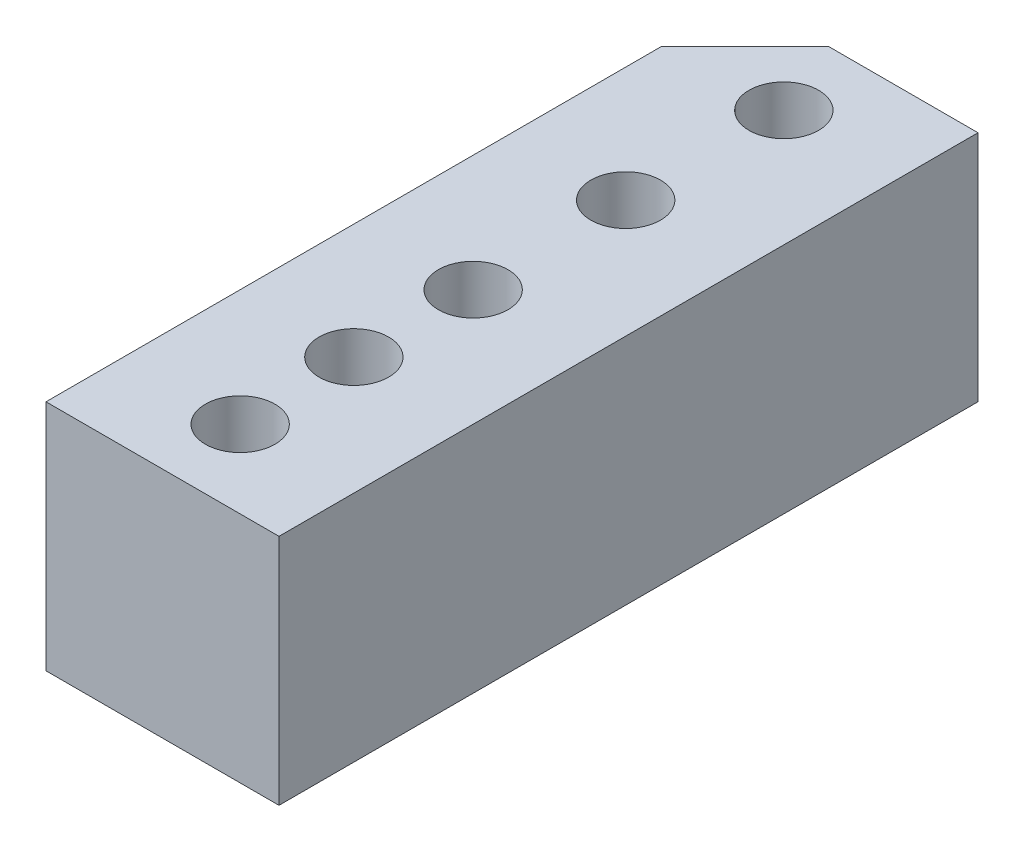
SolidWorks part; units mm, degrees
ref_plane "Front Plane" through (0, 0, 0) normal (0, 0, 1) x (1, 0, 0)
ref_plane "Top Plane" through (0, 0, 0) normal (0, 1, 0) x (1, 0, 0)
ref_plane "Right Plane" through (0, 0, 0) normal (1, 0, 0) x (0, 0, -1)
sketch "Sketch1" plane through (0, 0, 0) normal (0, 0, 1) x (1, 0, 0)
  line L1 (-4.7625, -4.7625) -> (4.7625, -4.7625)
  line L2 (-4.7625, -4.7625) -> (-4.7625, 4.7625)
  line L3 (-4.7625, 4.7625) -> (4.7625, 4.7625)
  line L4 (4.7625, -4.7625) -> (4.7625, 4.7625)
  line L5 (-4.7625, -4.7625) -> (4.7625, 4.7625) construction
  line L6 (-4.7625, 4.7625) -> (4.7625, -4.7625) construction
  point P0 (0, 0)
  dimension "D1" = 9.525
extrude "Extrude1" add sketch "Sketch1" along normal blind 28.575
hole_wizard "#4-40 Tapped Hole1" positions "3DSketch1" profile "Sketch2" tap size "#4-40" standard "Ansi Inch" end condition through all
sketch3d "3DSketch1"
  line L1 (-4.7625, 4.7625, 28.575) -> (-4.7625, 4.7625, 0) construction
  line L2 (4.7625, 4.7625, 28.575) -> (-4.7625, 4.7625, 28.575) construction
  point P0 (0, 4.7625, 3.175)
  point P2 (0, 4.7625, 15.875)
  point P4 (0, 4.7625, 25.4)
  dimension "D1" = 12.7
  dimension "D2" = 9.525
  dimension "D3" = 3.175
  dimension "D4" = 4.7625
sketch "Sketch2" plane through (0, 4.7625, 3.175) normal (1, 0, 0) x (0, 0, 1)
  line L0 (0, 0) -> (0, 9.525)
  line L1 (0, 9.525) -> (1.4224, 9.525)
  line L2 (1.4224, 9.525) -> (1.4224, 0)
  line L5 (1.4224, 0) -> (0, 0)
  line L11 (0, -6.35) -> (0, 107.95) construction
  dimension "Thread Major Dia." = 2.8448
  dimension "Thru Tap Drill Depth" = 9.525
hole_wizard "#4-40 Tapped Hole2" positions "3DSketch2" profile "Sketch3" tap size "#4-40" standard "Ansi Inch" end condition through all
sketch3d "3DSketch2"
  line L0 (-24.13, -6.3627, -10.795) -> (-24.13, -6.3627, 22.225) construction
  line L1 (-3.175, -6.3627, 41.275) -> (34.925, -6.3627, 41.275) construction
  point P0 (-0.0531, -4.7625, 20.6996)
  point P2 (-0.0531, -4.7625, 9.5871)
  dimension "D1" = 24.13
  dimension "D2" = 11.1125
  dimension "D3" = 20.6375
sketch "Sketch3" plane through (-0.0531, -4.7625, 20.6996) normal (1, 0, 0) x (0, 0, -1)
  line L0 (0, 0) -> (0, 9.525)
  line L1 (0, 9.525) -> (1.4224, 9.525)
  line L2 (1.4224, 9.525) -> (1.4224, 0)
  line L5 (1.4224, 0) -> (0, 0)
  line L11 (0, -6.35) -> (0, 107.95) construction
  dimension "Thread Major Dia." = 2.8448
  dimension "Thru Tap Drill Depth" = 9.525
chamfer "Chamfer1" distance 3.429 angle 45 1 edges at (-4.7625, 0, 0)
